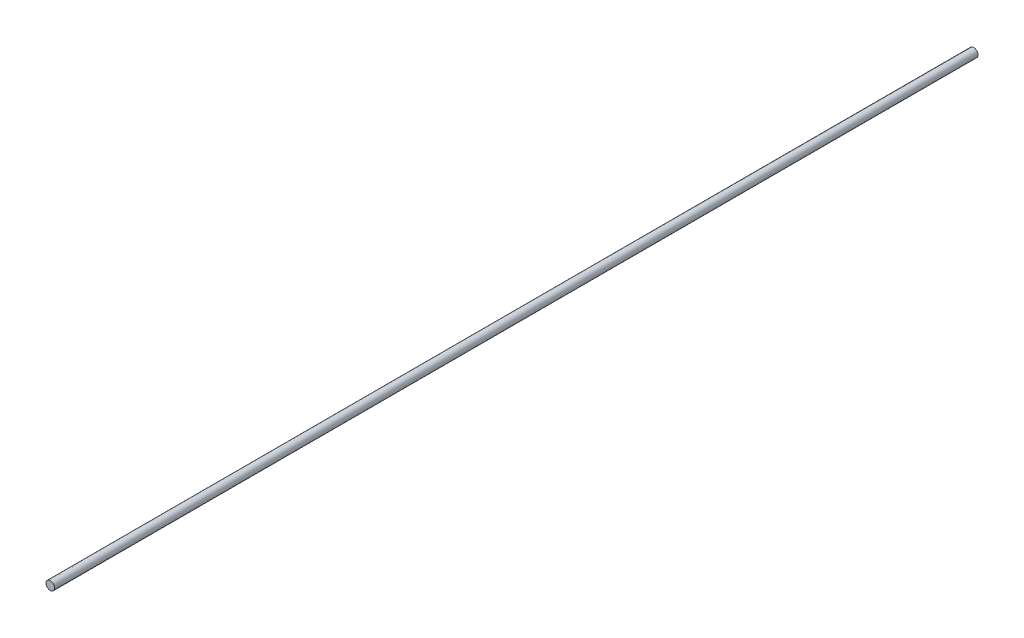
SolidWorks part; units mm, degrees
material "ASTM A36 Steel"
ref_plane "Front Plane" through (0, 0, 0) normal (0, 0, 1) x (1, 0, 0)
ref_plane "Top Plane" through (0, 0, 0) normal (0, 1, 0) x (1, 0, 0)
ref_plane "Right Plane" through (0, 0, 0) normal (1, 0, 0) x (0, 0, -1)
sketch "Sketch1" plane through (0, 0, 0) normal (0, 0, 1) x (1, 0, 0)
  circle A0 centre (0, 0) radius 7.5
  dimension "D1" = 15
extrude "Boss-Extrude1" add sketch "Sketch1" along normal blind 1615
sketch "Sketch2" plane through (0, 0, 0) normal (0, 0, -1) x (-1, 0, 0)
  circle A0 centre (0, 0) radius 4
  dimension "D1" = 8
extrude "Cut-Extrude1" cut sketch "Sketch2" against normal blind 40
